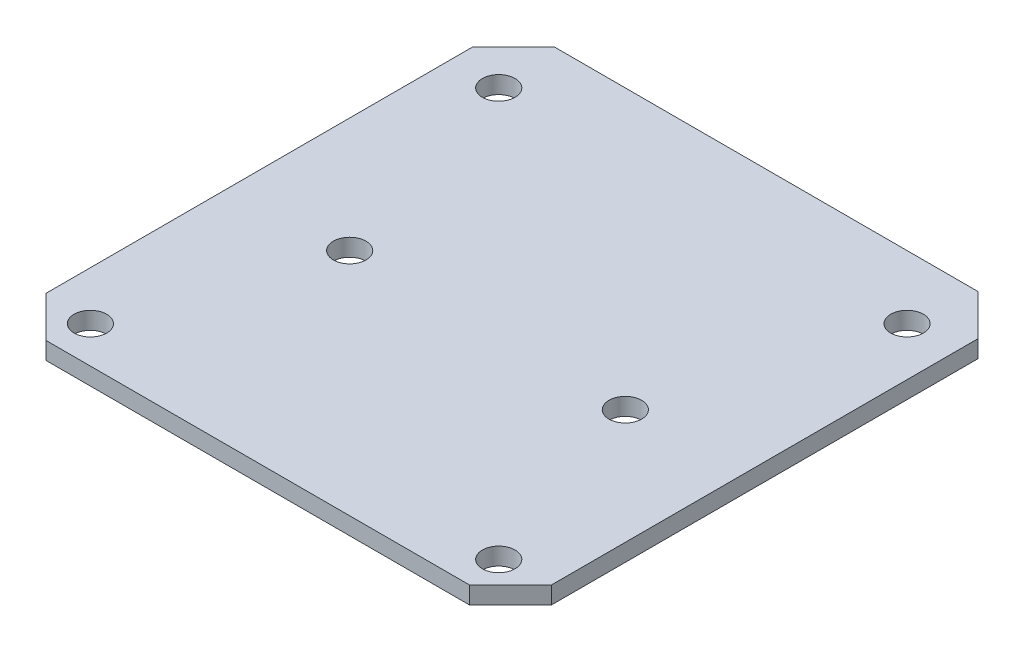
SolidWorks part; units mm, degrees
ref_plane "Front Plane" through (0, 0, 0) normal (0, 0, 1) x (1, 0, 0)
ref_plane "Top Plane" through (0, 0, 0) normal (0, 1, 0) x (1, 0, 0)
ref_plane "Right Plane" through (0, 0, 0) normal (1, 0, 0) x (0, 0, -1)
sketch "Sketch1" plane through (0, 0, 0) normal (0, 1, 0) x (1, 0, 0)
  line L1 (-24.75, 24.9) -> (24.75, 24.9)
  line L2 (-24.75, 24.9) -> (-24.75, -24.9)
  line L3 (-24.75, -24.9) -> (24.75, -24.9)
  line L4 (24.75, 24.9) -> (24.75, -24.9)
  line L5 (-24.75, 24.9) -> (24.75, -24.9) construction
  line L6 (-24.75, -24.9) -> (24.75, 24.9) construction
  point P0 (0, 0)
  dimension "D1" = 49.5
  dimension "D2" = 49.8
extrude "Boss-Extrude1" add sketch "Sketch1" along normal blind 1.7
hole_wizard "M3 Clearance Hole1" positions "Sketch2" profile "Sketch3" hole size "M3" standard "ANSI Metric" end condition through all
sketch "Sketch2" plane through (0, 1.7, 0) normal (0, 1, 0) x (1, 0, 0)
  point P0 (-20, 18.7)
  dimension "D1" = 20
  dimension "D2" = 18.7
sketch "Sketch3" plane through (-20, 1.7, -18.7) normal (1, 0, 0) x (0, 0, 1)
  line L0 (0, 0) -> (0, 1.7)
  line L1 (0, 1.7) -> (1.6, 1.7)
  line L2 (1.6, 1.7) -> (1.6, 0)
  line L5 (1.6, 0) -> (0, 0)
  line L11 (0, -6.35) -> (0, 107.95) construction
  dimension "Thru Hole Dia." = 3.2
  dimension "Thru Hole Depth" = 1.7
mirror "Mirror1" about plane through (0, 0, 0) normal (1, 0, 0) of "M3 Clearance Hole1"
pattern_linear "LPattern1" count 2 spacing 40 along (0, 0, 1) of "Mirror1", "M3 Clearance Hole1"
hole_wizard "M3 Clearance Hole2" positions "Sketch4" profile "Sketch5" hole size "M3" standard "ANSI Metric" end condition through all
sketch "Sketch4" plane through (0, 1.7, 0) normal (0, 1, 0) x (1, 0, 0)
  line L0 (-24.75, -24.9) -> (24.75, -24.9) construction
  point P0 (13.5, -2.4)
  dimension "D1" = 13.5
  dimension "D2" = 22.5
sketch "Sketch5" plane through (13.5, 1.7, 2.4) normal (1, 0, 0) x (0, 0, 1)
  line L0 (0, 0) -> (0, 1.7)
  line L1 (0, 1.7) -> (1.6, 1.7)
  line L2 (1.6, 1.7) -> (1.6, 0)
  line L5 (1.6, 0) -> (0, 0)
  line L11 (0, -6.35) -> (0, 107.95) construction
  dimension "Thru Hole Dia." = 3.2
  dimension "Thru Hole Depth" = 1.7
mirror "Mirror3" about plane through (0, 0, 0) normal (1, 0, 0) of "M3 Clearance Hole2"
chamfer "Chamfer1" distance 4 angle 45 4 edges at (-24.75, 0.85, 24.9) (24.75, 0.85, 24.9) (24.75, 0.85, -24.9) (-24.75, 0.85, -24.9)
